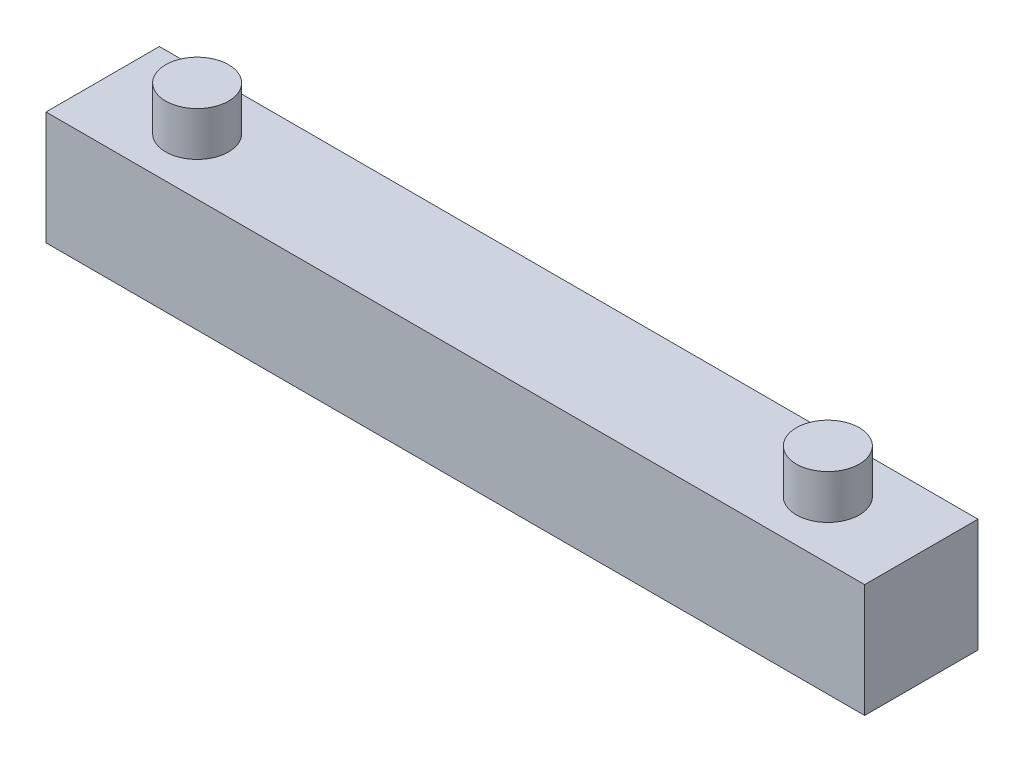
SolidWorks part; units mm, degrees
ref_plane "Front Plane" through (0, 0, 0) normal (0, 0, 1) x (1, 0, 0)
ref_plane "Top Plane" through (0, 0, 0) normal (0, 1, 0) x (1, 0, 0)
ref_plane "Right Plane" through (0, 0, 0) normal (1, 0, 0) x (0, 0, -1)
sketch "Sketch1" plane through (0, 0, 0) normal (0, 0, 1) x (1, 0, 0)
  line L0 (0, 0) -> (65, 0)
  line L1 (65, 0) -> (65, 9)
  line L2 (65, 9) -> (0, 9)
  line L3 (0, 9) -> (0, 0)
  dimension "D1" = 65
  dimension "D2" = 9
extrude "Boss-Extrude1" add sketch "Sketch1" along normal blind 9
sketch "Sketch2" plane through (0, 9, 0) normal (0, 1, 0) x (1, 0, 0)
  line L0 (65, -9) -> (65, 0) construction
  line L1 (0, -9) -> (0, 0) construction
  line L2 (65, -9) -> (0, -9) construction
  line L3 (65, 0) -> (0, 0) construction
  circle A0 centre (7.5005, -4.5) radius 2.5
  circle A1 centre (57.5004, -4.4224) radius 2.5
  point P4 (65, -4.5)
  point P7 (65, -4.5)
  point P8 (0, -4.5)
  dimension "D8" = 5
  dimension "D9" = 5
  dimension "D1" = 50
  dimension "D2" = 7.5
  dimension "D3" = 7.5005
  dimension "D4" = 9
  dimension "D5" = 4.5
  dimension "D6" = 4.5
  dimension "D7" = 4.5776
extrude "Boss-Extrude2" add sketch "Sketch2" along normal blind 3.5
